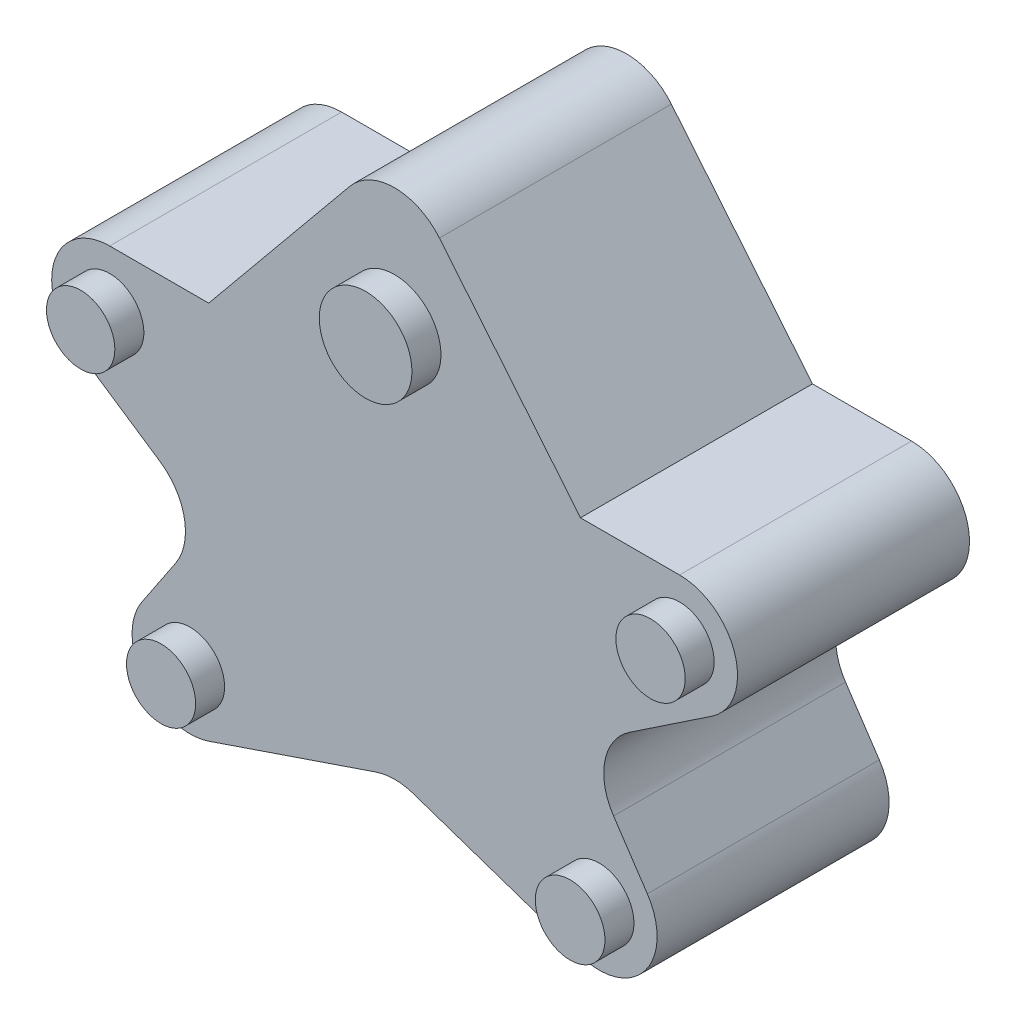
SolidWorks part; units mm, degrees
material "PC High Viscosity"
ref_plane "Front Plane" through (0, 0, 0) normal (0, 0, 1) x (1, 0, 0)
ref_plane "Top Plane" through (0, 0, 0) normal (0, 1, 0) x (1, 0, 0)
ref_plane "Right Plane" through (0, 0, 0) normal (1, 0, 0) x (0, 0, -1)
sketch "Sketch2" plane through (0, 0, 0) normal (0, 0, 1) x (1, 0, 0)
  line L0 (10.1619, 60.5263) -> (60.1619, 60.5263)
  line L1 (60.1619, 60.5263) -> (92.2201, 99.5394)
  line L2 (10.1619, 60.5263) -> (60.0271, 27.1578)
  line L3 (60.0271, 27.1578) -> (32.2201, -14.3966)
  line L5 (32.2201, -14.3966) -> (92.2201, 6.015)
  line L6 (152.2201, -14.3966) -> (92.2201, 6.015)
  line L7 (124.413, 27.1578) -> (152.2201, -14.3966)
  line L8 (174.2783, 60.5263) -> (124.413, 27.1578)
  line L9 (174.2783, 60.5263) -> (124.2783, 60.5263)
  line L10 (124.2783, 60.5263) -> (92.2201, 99.5394)
  dimension "D1" = 50
  dimension "D2" = 50.495
  dimension "D3" = 60
  dimension "D4" = 50
  dimension "D5" = 60
extrude "Boss-Extrude1" add sketch "Sketch2" along normal blind 40
fillet "Fillet1" radius 10 8 edges at (60.0271, 27.1578, 20) (124.413, 27.1578, 20) (152.2201, -14.3966, 20) (92.2201, 6.015, 20) (32.2201, -14.3966, 20) (92.2201, 99.5394, 20) (10.1619, 60.5263, 20) (174.2783, 60.5263, 20)
sketch "Sketch3" plane through (0, 0, 40) normal (0, 0, 1) x (1, 0, 0)
  circle A1 centre (92.2201, 72.8316) radius 7.9896
  circle A2 centre (43.0867, 50.5263) radius 5.8929
  circle A3 centre (56.9507, 4.5795) radius 5.9603
  circle A4 centre (127.4894, 4.5795) radius 6.0037
  circle A5 centre (141.3534, 50.5263) radius 5.9725
  point P16 (85.017, 72.8316)
  point P17 (192.9375, 54.7858)
extrude "Boss-Extrude2" add sketch "Sketch3" along normal blind 5
sketch "Sketch5" plane through (0, 0, 40) normal (0, 0, 1) x (1, 0, 0)
